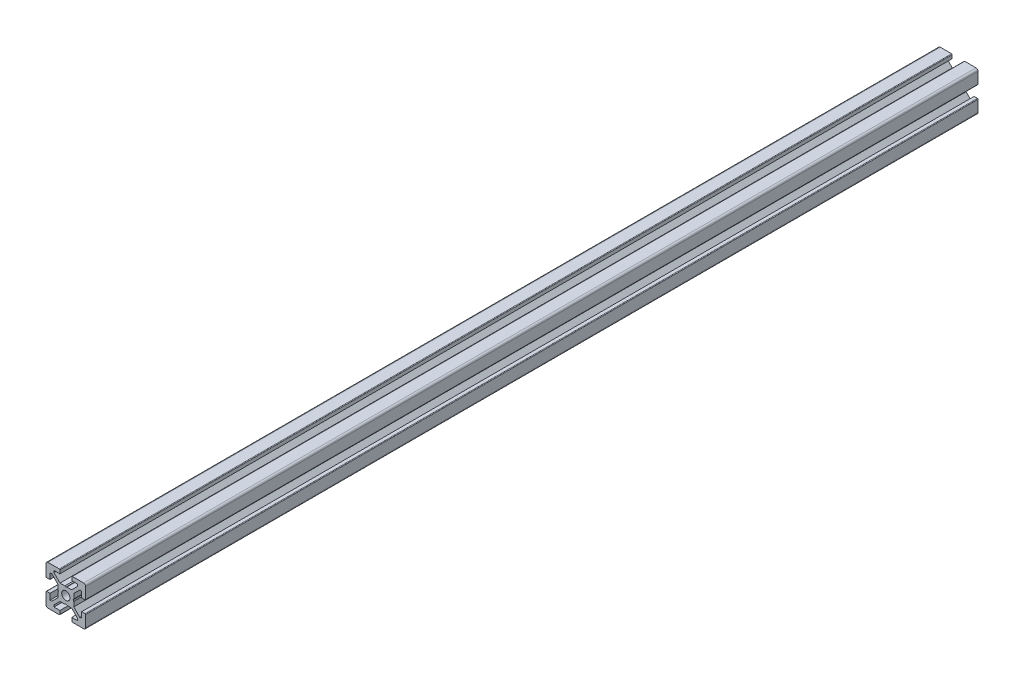
SolidWorks part; units mm, degrees
ref_plane "Front" through (0, 0, 0) normal (0, 0, 1) x (1, 0, 0)
ref_plane "Top" through (0, 0, 0) normal (0, 1, 0) x (1, 0, 0)
ref_plane "Right" through (0, 0, 0) normal (1, 0, 0) x (0, 0, -1)
ref_plane "Plane1" through (0, 0, 0) normal (0, 0, 1) x (1, 0, 0)
sketch "Sketch1" plane through (0, 0, 0) normal (0, 0, 1) x (1, 0, 0)
  line L0 (-10, 9) -> (-10, 3.3)
  line L1 (-9.7, 3) -> (-8, 3)
  line L2 (-8, 3) -> (-8, 6)
  line L3 (-8, 6) -> (-7.0607, 6)
  line L4 (-7.0607, 6) -> (-4, 2.9393)
  line L5 (-4, 2.9393) -> (-4, 0.5196)
  line L6 (-4, 0.5196) -> (-3.7, 0)
  line L7 (-3.7, 0) -> (-4, -0.5196)
  line L8 (-4, -0.5196) -> (-4, -2.9393)
  line L9 (-4, -2.9393) -> (-7.0607, -6)
  line L10 (-7.0607, -6) -> (-8, -6)
  line L11 (-8, -6) -> (-8, -3)
  line L12 (-8, -3) -> (-9.7, -3)
  line L13 (-10, -3.3) -> (-10, -9)
  line L14 (-9, -10) -> (-3.3, -10)
  line L15 (-3, -9.7) -> (-3, -8)
  line L16 (-3, -8) -> (-6, -8)
  line L17 (-6, -8) -> (-6, -7.0607)
  line L18 (-6, -7.0607) -> (-2.9393, -4)
  line L19 (-2.9393, -4) -> (-0.5196, -4)
  line L20 (-0.5196, -4) -> (0, -3.7)
  line L21 (0, -3.7) -> (0.5196, -4)
  line L22 (0.5196, -4) -> (2.9393, -4)
  line L23 (2.9393, -4) -> (6, -7.0607)
  line L24 (6, -7.0607) -> (6, -8)
  line L25 (6, -8) -> (3, -8)
  line L26 (3, -8) -> (3, -9.7)
  line L27 (3.3, -10) -> (9, -10)
  line L28 (10, -9) -> (10, -3.3)
  line L29 (9.7, -3) -> (8, -3)
  line L30 (8, -3) -> (8, -6)
  line L31 (8, -6) -> (7.0606, -6)
  line L32 (7.0606, -6) -> (4, -2.9393)
  line L33 (4, -2.9393) -> (4, -0.5196)
  line L34 (4, -0.5196) -> (3.7, 0)
  line L35 (3.7, 0) -> (4, 0.5196)
  line L36 (4, 0.5196) -> (4, 2.9393)
  line L37 (4, 2.9393) -> (7.0607, 6)
  line L38 (7.0607, 6) -> (8, 6)
  line L39 (8, 6) -> (8, 3)
  line L40 (8, 3) -> (9.7, 3)
  line L41 (10, 3.3) -> (10, 9)
  line L42 (9, 10) -> (3.3, 10)
  line L43 (3, 9.7) -> (3, 8)
  line L44 (3, 8) -> (6, 8)
  line L45 (6, 8) -> (6, 7.0607)
  line L46 (6, 7.0607) -> (2.9393, 4)
  line L47 (2.9393, 4) -> (0.5196, 4)
  line L48 (0.5196, 4) -> (0, 3.7)
  line L49 (0, 3.7) -> (-0.5196, 4)
  line L50 (-0.5196, 4) -> (-2.9394, 4)
  line L51 (-2.9394, 4) -> (-6, 7.0606)
  line L52 (-6, 7.0606) -> (-6, 8)
  line L53 (-6, 8) -> (-3, 8)
  line L54 (-3, 8) -> (-3, 9.7)
  line L55 (-3.3, 10) -> (-9, 10)
  arc A0 (-10, 3.3) -> (-9.7, 3) centre (-9.7, 3.3) ccw
  arc A1 (-9.7, -3) -> (-10, -3.3) centre (-9.7, -3.3) ccw
  arc A2 (-10, -9) -> (-9, -10) centre (-9, -9) ccw
  arc A3 (-3.3, -10) -> (-3, -9.7) centre (-3.3, -9.7) ccw
  arc A4 (3, -9.7) -> (3.3, -10) centre (3.3, -9.7) ccw
  arc A5 (9, -10) -> (10, -9) centre (9, -9) ccw
  arc A6 (10, -3.3) -> (9.7, -3) centre (9.7, -3.3) ccw
  arc A7 (9.7, 3) -> (10, 3.3) centre (9.7, 3.3) ccw
  arc A8 (10, 9) -> (9, 10) centre (9, 9) ccw
  arc A9 (3.3, 10) -> (3, 9.7) centre (3.3, 9.7) ccw
  arc A10 (-3, 9.7) -> (-3.3, 10) centre (-3.3, 9.7) ccw
  arc A11 (-9, 10) -> (-10, 9) centre (-9, 9) ccw
extrude "Boss-Extrude1" add sketch "Sketch1" against normal blind 450
ref_plane "Plane2" through (0, 0, 0) normal (1, 0, 0) x (0, 0, -1)
sketch "Sketch2" plane through (0, 0, 0) normal (1, 0, 0) x (0, 0, -1)
  line L0 (0, 0) -> (0, 2.1)
  line L1 (0, 2.1) -> (450, 2.1)
  line L2 (450, 2.1) -> (450, 0)
  line L3 (450, 0) -> (0, 0)
  line L4 (450, 0) -> (0, 0) construction
revolve "Cut-Revolve1" cut sketch "Sketch2" angle 360 about L4
